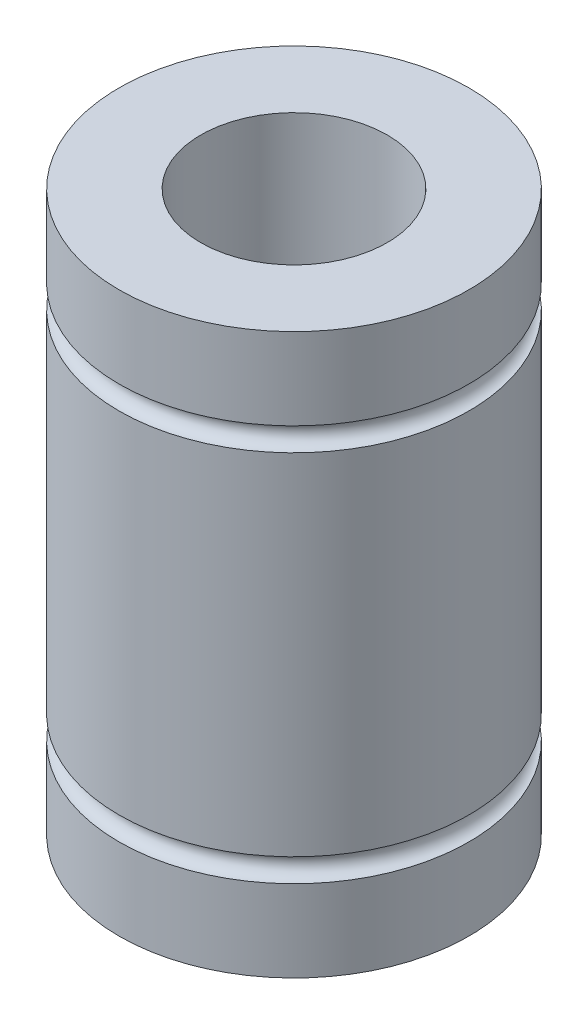
SolidWorks part; units mm, degrees
ref_plane "Front" through (0, 0, 0) normal (0, 0, 1) x (1, 0, 0)
ref_plane "Top" through (0, 0, 0) normal (0, 1, 0) x (1, 0, 0)
ref_plane "Right" through (0, 0, 0) normal (1, 0, 0) x (0, 0, -1)
sketch "Sketch1" plane through (0, 0, 0) normal (0, 1, 0) x (1, 0, 0)
  circle A0 centre (0, 0) radius 4
  circle A1 centre (0, 0) radius 7.5
extrude "Boss-Extrude1" add sketch "Sketch1" along normal blind 24
sketch "Sketch2" plane through (0, 0, 0) normal (0, 0, 1) x (1, 0, 0)
  line L1 (-9.3225, 12) -> (13.9837, 12) construction
  line L4 (0, 20.782) -> (0, 3.4882) construction
  line L5 (7.5, 0) -> (7.5, 24) construction
  line L6 (-7.5, 0) -> (7.5, 0) construction
  circle A2 centre (7.5, 4) radius 0.5
  circle A3 centre (7.5, 20) radius 0.5
  dimension "D1" = 4
revolve "Cut-Revolve1" cut sketch "Sketch2" angle 360 about L4
